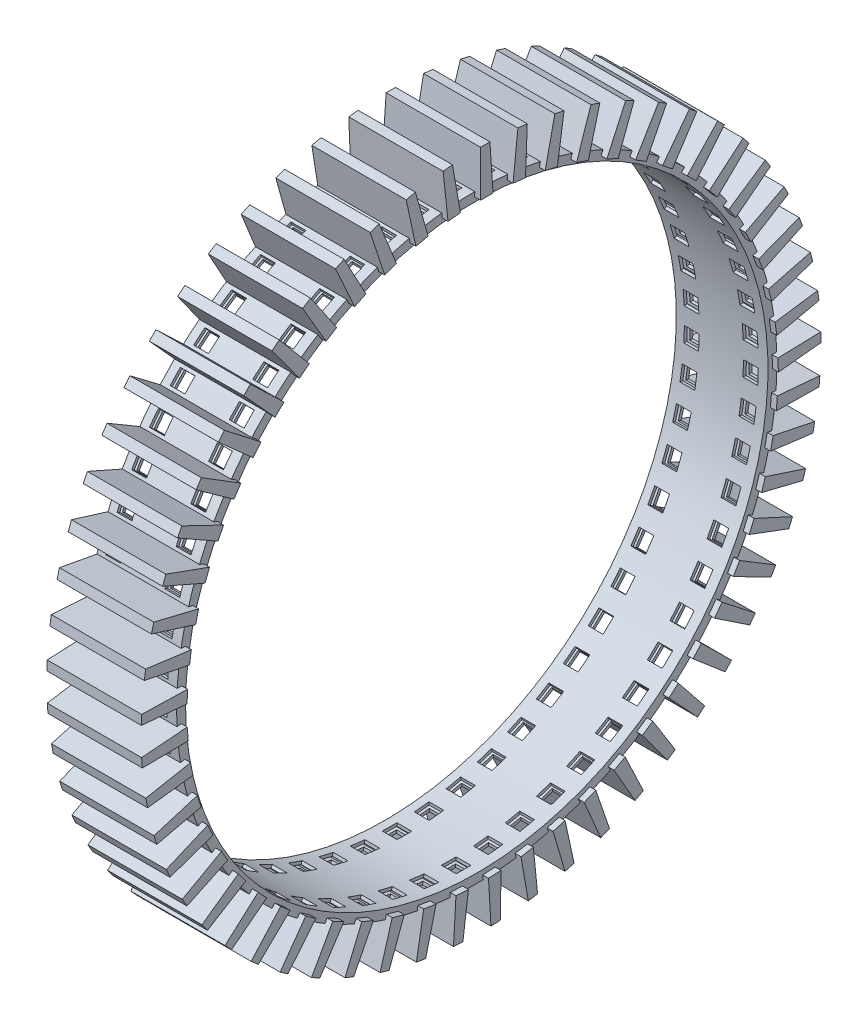
SolidWorks part; units mm, degrees
ref_plane "Front Plane" through (0, 0, 0) normal (0, 0, 1) x (1, 0, 0)
ref_plane "Top Plane" through (0, 0, 0) normal (0, 1, 0) x (1, 0, 0)
ref_plane "Right Plane" through (0, 0, 0) normal (1, 0, 0) x (0, 0, -1)
sketch "Sketch3" plane through (0, 0, 0) normal (0, 0, 1) x (1, 0, 0)
  line L0 (0, 0) -> (0, 99.029) construction
  line L1 (-16.6667, 101.029) -> (13.3333, 101.029)
  line L2 (-16.6667, 101.029) -> (-16.6667, 99.029)
  line L3 (-16.6667, 99.029) -> (13.3333, 99.029)
  line L4 (13.3333, 101.029) -> (13.3333, 99.029)
  line L5 (0, 0) -> (-41.6407, 0)
  line L6 (55.7195, 0) -> (-60.5324, 0) construction
  dimension "D1" = 30
  dimension "D2" = 2
  dimension "D3" = 99.029
revolve "Revolve-Thin1" add sketch "Sketch3" angle 360 mid plane about L6
sketch "Sketch4" plane through (0, 0, 0) normal (0, 0, 1) x (1, 0, 0)
  line L0 (13.8333, -0.8003) -> (-17.1667, -0.8003) construction
  line L9 (13.8333, -101.529) -> (13.8333, 101.529) construction
  line L10 (-17.1667, 101.529) -> (-17.1667, -101.529) construction
  point P5 (0, 0)
sketch "Sketch5" plane through (0, 0, 0) normal (0, 1, 0) x (1, 0, 0)
  point P11 (-1.9396, -4.2062)
ref_plane "Plane1" through (0, 120, 0) normal (0, -1, 0) x (-1, 0, 0)
sketch "Sketch8" plane through (0, 120, 0) normal (0, -1, 0) x (-1, 0, 0)
  line L2 (-10.5616, -6.6971) -> (-5.56, -6.6971)
  line L3 (-10.5616, -6.6971) -> (-10.5616, -1.7153)
  line L4 (-10.5616, -1.7153) -> (-5.56, -1.7153)
  line L5 (-5.56, -6.6971) -> (-5.56, -1.7153)
  line L6 (-10.5616, -6.6971) -> (-5.56, -1.7153) construction
  line L7 (-10.5616, -1.7153) -> (-5.56, -6.6971) construction
  line L8 (14.4409, -6.6971) -> (9.4393, -6.6971)
  line L9 (14.4409, -6.6971) -> (14.4409, -1.7153)
  line L10 (14.4409, -1.7153) -> (9.4393, -1.7153)
  line L11 (9.4393, -6.6971) -> (9.4393, -1.7153)
  point P4 (1.9396, -4.2062)
extrude "Cut-Extrude7" cut sketch "Sketch8" along normal blind 50 contours L3 L2 L5 L4 | L8 L11 L10 L9
pattern_circular "CirPattern3" count 57 over 360 about axis through (0, 0, 0) along (1, 0, 0) of "Cut-Extrude7"
ref_plane "Plane2" through (0, 100, 0) normal (0, 1, 0) x (1, 0, 0)
sketch "Sketch11" plane through (0, 100, 0) normal (0, 1, 0) x (1, 0, 0)
  line L8 (-17.1667, 101.529) -> (-17.1667, -101.529) construction
  line L9 (-17.1667, -0.7126) -> (15.8163, -0.7126)
  line L10 (-17.1667, -0.7126) -> (-17.1667, 3.5202)
  line L11 (-17.1667, 3.5202) -> (15.8163, 3.5202)
  line L12 (15.8163, -0.7126) -> (15.8163, 3.5202)
extrude "Boss-Extrude3" add sketch "Sketch11" along normal blind 15 draft 2
pattern_circular "CirPattern4" count 57 over 360 about axis through (0, 0, 0) along (1, 0, 0) of "Boss-Extrude3"
